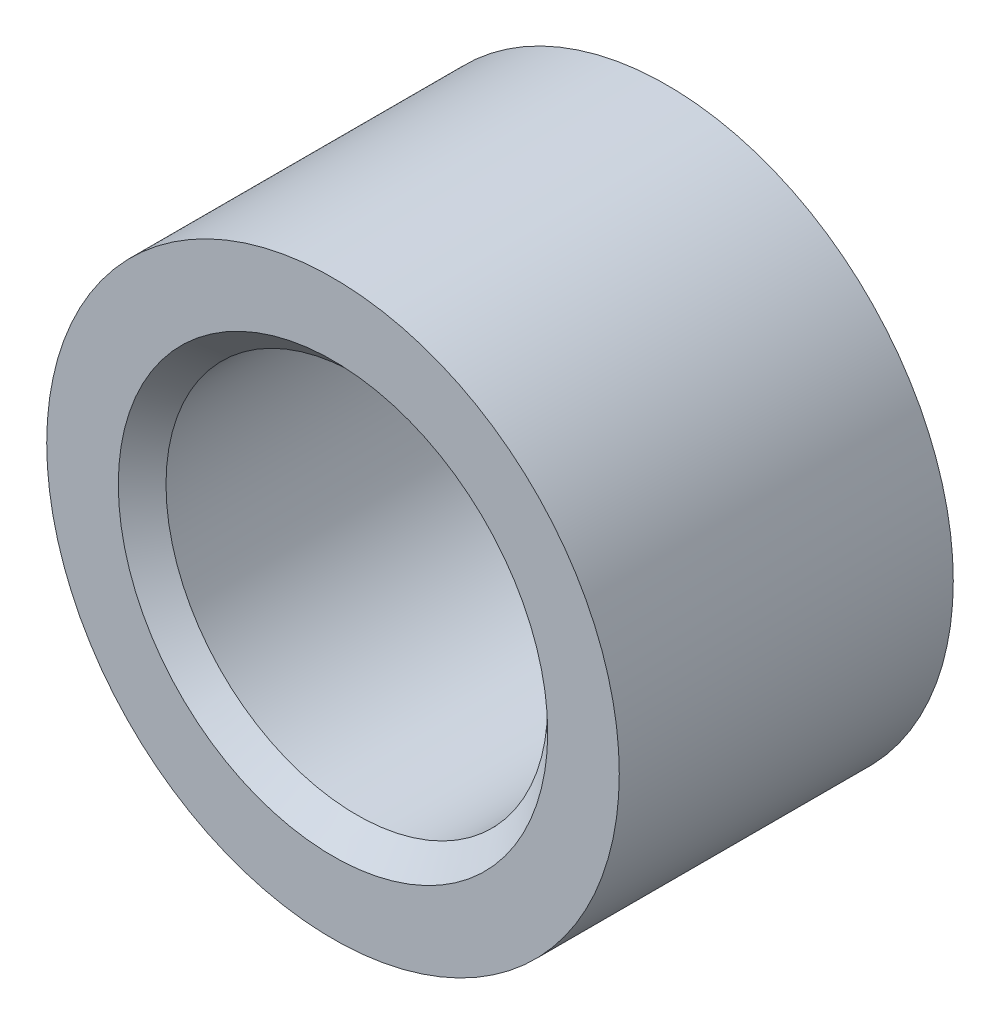
SolidWorks part; units mm, degrees
ref_plane "Front Plane" through (0, 0, 0) normal (0, 0, 1) x (1, 0, 0)
ref_plane "Top Plane" through (0, 0, 0) normal (0, 1, 0) x (1, 0, 0)
ref_plane "Right Plane" through (0, 0, 0) normal (1, 0, 0) x (0, 0, -1)
sketch "Sketch1" plane through (0, 0, 0) normal (0, 0, 1) x (1, 0, 0)
  circle A0 centre (0, 0) radius 4
  circle A1 centre (0, 0) radius 6
  dimension "D1" = 8
  dimension "D2" = 12
extrude "Boss-Extrude1" add sketch "Sketch1" along normal mid plane 7
chamfer "Chamfer1" distance 0.5 angle 45 2 edges at (4, 0, -3.5) (4, 0, 3.5)
